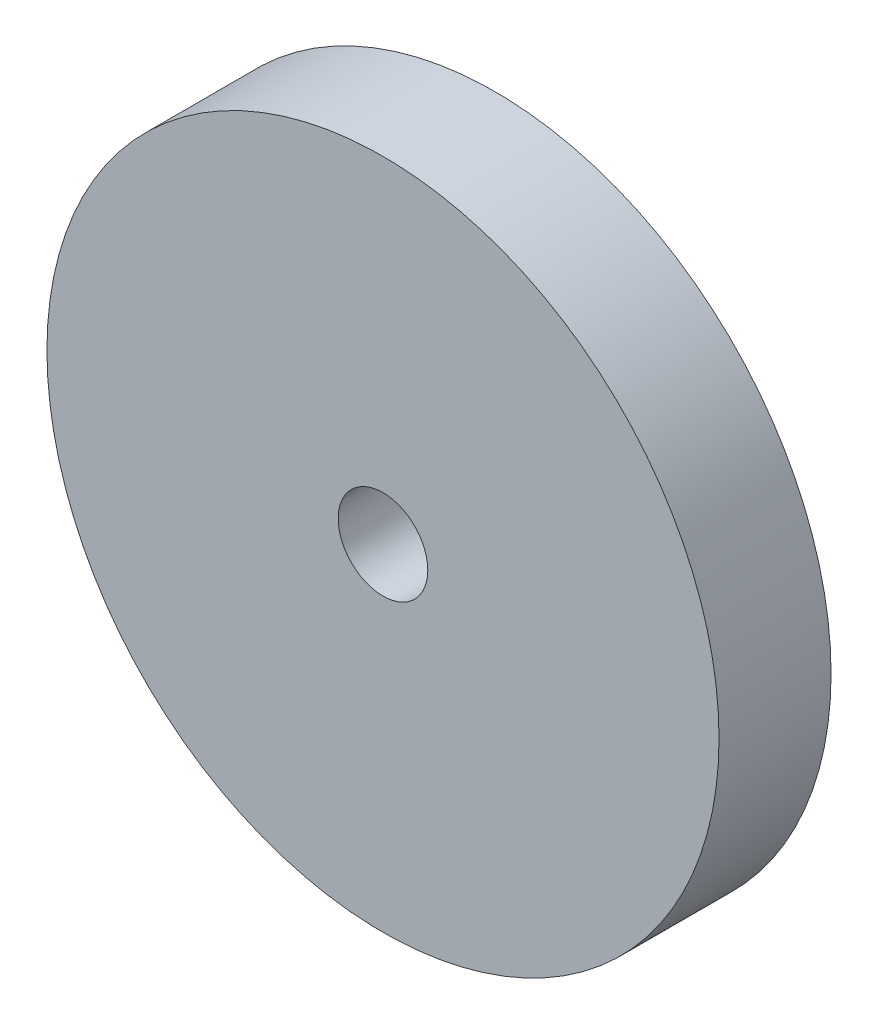
SolidWorks part; units mm, degrees
ref_plane "Front Plane" through (0, 0, 0) normal (0, 0, 1) x (1, 0, 0)
ref_plane "Top Plane" through (0, 0, 0) normal (0, 1, 0) x (1, 0, 0)
ref_plane "Right Plane" through (0, 0, 0) normal (1, 0, 0) x (0, 0, -1)
sketch "Sketch1" plane through (0, 0, 0) normal (0, 0, 1) x (1, 0, 0)
  circle A0 centre (0, 0) radius 20
  circle A1 centre (0, 0) radius 150
  dimension "D1" = 300
  dimension "D2" = 40
extrude "Boss-Extrude1" add sketch "Sketch1" along normal blind 50
